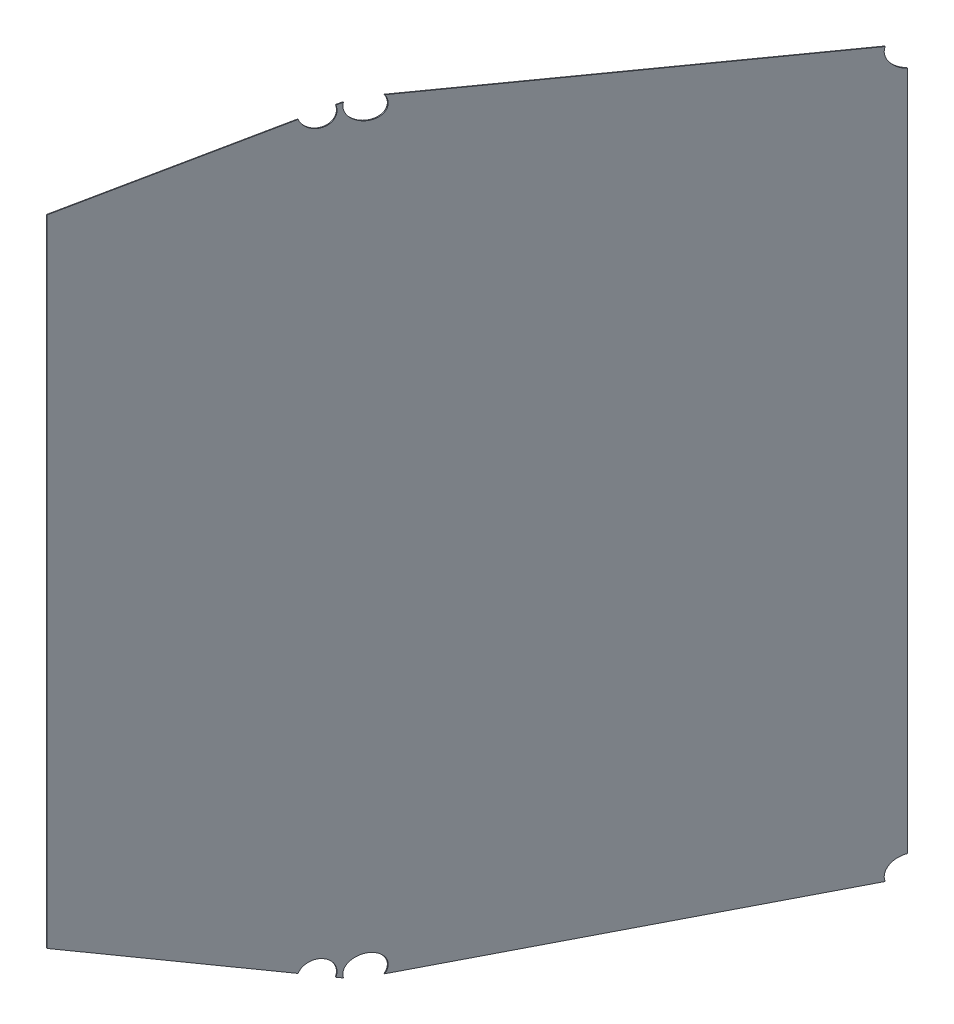
SolidWorks part; units mm, degrees
material "6061 Alloy"
ref_plane "X-Y Datum" through (0, 0, 0) normal (0, 0, 1) x (1, 0, 0)
ref_plane "X-Z Datum" through (0, 0, 0) normal (0, 1, 0) x (1, 0, 0)
ref_plane "Y-Z Datum" through (0, 0, 0) normal (1, 0, 0) x (0, 0, -1)
ref_plane "Plane1" through (348.7789, 0, 212.3298) normal (0.8542, 0, 0.52) x (0.52, 0, -0.8542)
sketch "Sketch3" plane through (348.7789, 0, 212.3298) normal (0.8542, 0, 0.52) x (0.52, 0, -0.8542)
  line L6 (310.9836, 336.55) -> (-63.6664, 356.1846)
  line L7 (310.9836, 0) -> (-273.2164, 0)
  line L8 (310.9836, -336.55) -> (310.9836, 336.55)
  line L9 (-63.6664, 356.1846) -> (-273.2164, 296.3149)
  line L10 (-273.2164, 296.3149) -> (-273.2164, -296.3149)
  line L11 (-63.6664, -356.1846) -> (-273.2164, -296.3149)
  line L12 (310.9836, -336.55) -> (-63.6664, -356.1846)
  dimension "D1" = 336.55
  dimension "D2" = 584.2
  dimension "D3" = 93
  dimension "D5" = 217.9348
extrude "Boss-Extrude1" add sketch "Sketch3" along normal mid plane 0.635 contours L9 L10 L7 L8 L6 | L12 L8 L7 L10 L11
ref_plane "Plane2" through (381.6853, 370.332, -52.6063) normal (-0.9562, 0.2928, 0) x (0, 0, 1)
sketch "Sketch4" plane through (381.6853, 370.332, -52.6063) normal (-0.9562, 0.2928, 0) x (0, 0, 1)
  circle A0 centre (0, 0) radius 12.8905
  dimension "D1" = 25.781
extrude "Cut-Extrude1" cut sketch "Sketch4" against normal blind 152.4
ref_plane "Plane3" through (197.5353, 368.3599, 264.8937) normal (-0.9875, 0.1543, 0.0309) x (0.0305, -0.0048, 0.9995)
sketch "Sketch5" plane through (197.5353, 368.3599, 264.8937) normal (-0.9875, 0.1543, 0.0309) x (0.0305, -0.0048, 0.9995)
  circle A0 centre (0, 0) radius 12.8905
  dimension "D1" = 25.781
extrude "Cut-Extrude2" cut sketch "Sketch5" against normal blind 152.4
ref_plane "Plane4" through (197.5353, 368.3599, 264.8937) normal (-0.9581, 0.1805, -0.2224) x (-0.2185, 0.0412, 0.975)
sketch "Sketch6" plane through (197.5353, 368.3599, 264.8937) normal (-0.9581, 0.1805, -0.2224) x (-0.2185, 0.0412, 0.975)
  circle A0 centre (0, 0) radius 12.8905
  dimension "D1" = 25.781
extrude "Cut-Extrude3" cut sketch "Sketch6" against normal blind 152.4
mirror "Mirror1" about plane through (0, 0, 0) normal (0, 1, 0) of "Cut-Extrude3", "Cut-Extrude2", "Cut-Extrude1"
